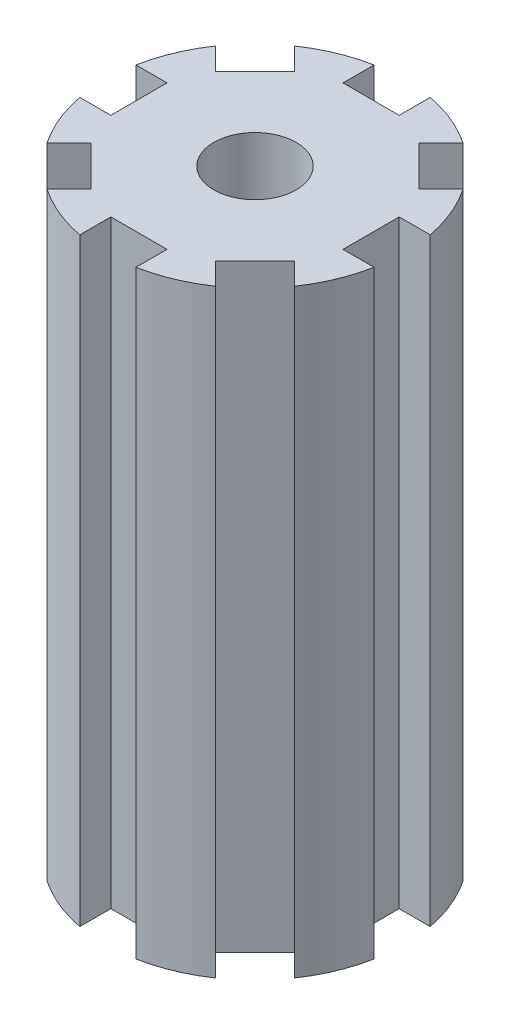
SolidWorks part; units mm, degrees
ref_plane "Front Plane" through (0, 0, 0) normal (0, 0, 1) x (1, 0, 0)
ref_plane "Top Plane" through (0, 0, 0) normal (0, 1, 0) x (1, 0, 0)
ref_plane "Right Plane" through (0, 0, 0) normal (1, 0, 0) x (0, 0, -1)
sketch "Sketch1" plane through (0, 0, 0) normal (0, 1, 0) x (0, 0, -1)
  circle A0 centre (0, 0) radius 12.7
  dimension "D1" = 25.4
extrude "Boss-Extrude1" add sketch "Sketch1" against normal blind 50.8 contours A0
sketch "Sketch2" plane through (0, 0, 0) normal (0, 1, 0) x (0, 0, -1)
  line L0 (12.6846, 9.317) -> (9.317, 12.6846)
  line L1 (2.3813, 9.8425) -> (-2.3813, 9.8425)
  line L2 (2.3813, 9.8425) -> (2.3813, 15.5575)
  line L3 (2.3813, 15.5575) -> (-2.3813, 15.5575)
  line L4 (-2.3813, 9.8425) -> (-2.3813, 15.5575)
  line L5 (2.3813, 9.8425) -> (-2.3813, 15.5575) construction
  line L6 (2.3813, 15.5575) -> (-2.3813, 9.8425) construction
  line L7 (5.2759, 8.6435) -> (9.317, 12.6846)
  line L8 (8.6435, 5.2759) -> (12.6846, 9.317)
  line L9 (8.6435, 5.2759) -> (5.2759, 8.6435)
  line L10 (15.5575, -2.3812) -> (15.5575, 2.3813)
  line L11 (9.8425, 2.3813) -> (15.5575, 2.3813)
  line L12 (9.8425, -2.3812) -> (15.5575, -2.3812)
  line L13 (9.8425, -2.3812) -> (9.8425, 2.3813)
  line L14 (9.317, -12.6846) -> (12.6846, -9.317)
  line L15 (8.6435, -5.2759) -> (12.6846, -9.317)
  line L16 (5.2759, -8.6435) -> (9.317, -12.6846)
  line L17 (5.2759, -8.6435) -> (8.6435, -5.2759)
  line L18 (-2.3812, -15.5575) -> (2.3813, -15.5575)
  line L19 (2.3813, -9.8425) -> (2.3813, -15.5575)
  line L20 (-2.3812, -9.8425) -> (-2.3812, -15.5575)
  line L21 (-2.3812, -9.8425) -> (2.3813, -9.8425)
  line L22 (-12.6846, -9.317) -> (-9.317, -12.6846)
  line L23 (-5.2759, -8.6435) -> (-9.317, -12.6846)
  line L24 (-8.6435, -5.2759) -> (-12.6846, -9.317)
  line L25 (-8.6435, -5.2759) -> (-5.2759, -8.6435)
  line L26 (-15.5575, 2.3812) -> (-15.5575, -2.3813)
  line L27 (-9.8425, -2.3813) -> (-15.5575, -2.3813)
  line L28 (-9.8425, 2.3812) -> (-15.5575, 2.3812)
  line L29 (-9.8425, 2.3812) -> (-9.8425, -2.3813)
  line L30 (-9.317, 12.6846) -> (-12.6846, 9.317)
  line L31 (-8.6435, 5.2759) -> (-12.6846, 9.317)
  line L32 (-5.2759, 8.6435) -> (-9.317, 12.6846)
  line L33 (-5.2759, 8.6435) -> (-8.6435, 5.2759)
  circle A0 centre (0, 0) radius 12.7 construction
  circle A1 centre (0, 0) radius 3.4925
  point P0 (0, 12.7)
  point P9 (0, 0)
  point P38 (0, 0)
  dimension "D4" = 6.985
  dimension "D1" = 5.715
  dimension "D2" = 4.7625
  dimension "D3" = 8
extrude "Cut-Extrude1" cut sketch "Sketch2" against normal blind 109.22
